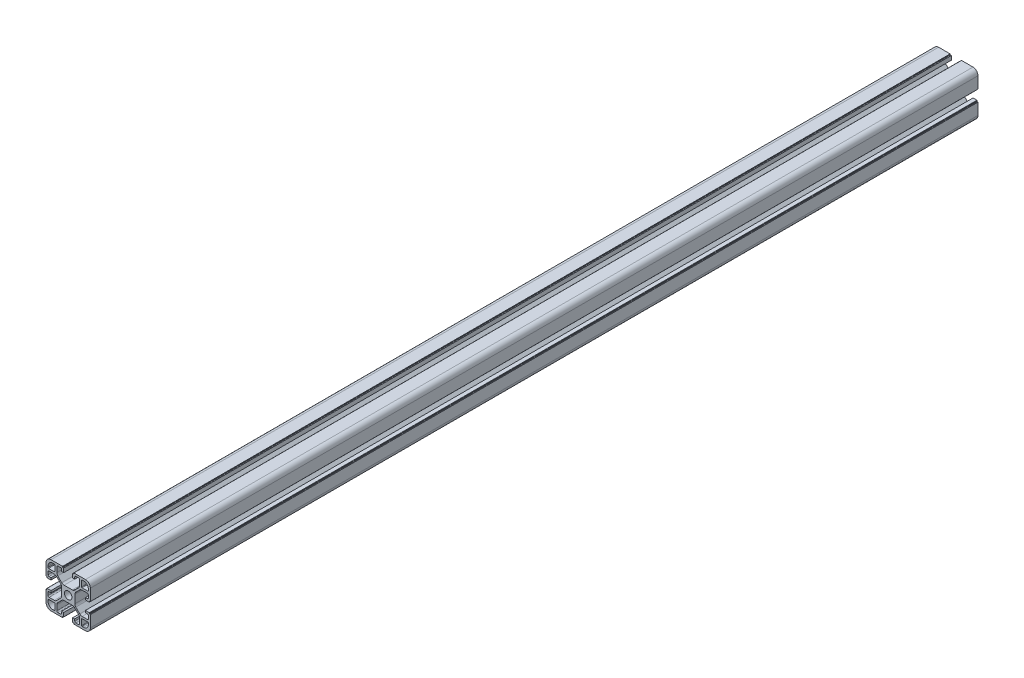
SolidWorks part; units mm, degrees
ref_plane "Front Plane" through (0, 0, 0) normal (0, 0, 1) x (1, 0, 0)
ref_plane "Top Plane" through (0, 0, 0) normal (0, 1, 0) x (1, 0, 0)
ref_plane "Right Plane" through (0, 0, 0) normal (1, 0, 0) x (0, 0, -1)
sketch "Sketch2" plane through (0, 0, 0) normal (0, 0, 1) x (1, 0, 0)
  line L0 (84.1702, 31.7204) -> (84.1702, 42.1204)
  line L1 (44.1702, 62.7204) -> (44.1702, 52.3204)
  line L2 (48.6702, 27.2204) -> (59.0702, 27.2204)
  line L3 (79.6702, 67.2204) -> (69.2702, 67.2204)
  line L4 (84.1702, 52.3204) -> (84.1702, 62.7204)
  line L6 (44.1702, 42.1204) -> (44.1702, 31.7204)
  line L7 (69.2702, 27.2204) -> (79.6702, 27.2204)
  line L10 (44.1702, 42.1204) -> (44.7702, 42.1204)
  line L11 (44.9702, 42.3204) -> (44.9702, 42.9204)
  line L12 (48.6702, 43.1204) -> (45.1702, 43.1204)
  line L13 (48.6702, 41.3204) -> (48.6702, 43.1204)
  line L14 (46.9702, 41.3204) -> (48.6702, 41.3204)
  line L15 (45.9702, 37.9704) -> (45.9702, 40.3204)
  line L16 (51.6169, 36.9704) -> (46.9702, 36.9704)
  line L17 (57.2915, 41.4024) -> (53.7382, 37.8491)
  line L18 (58.1702, 50.9171) -> (58.1702, 43.5237)
  line L19 (53.7382, 56.5917) -> (57.2915, 53.0384)
  line L20 (46.9702, 57.4704) -> (51.6169, 57.4704)
  line L21 (45.9702, 54.1204) -> (45.9702, 56.4704)
  line L22 (48.6702, 53.1204) -> (46.9702, 53.1204)
  line L23 (48.6702, 51.3204) -> (48.6702, 53.1204)
  line L24 (45.1702, 51.3204) -> (48.6702, 51.3204)
  line L25 (44.9702, 51.5204) -> (44.9702, 52.1204)
  line L26 (44.7702, 52.3204) -> (44.1702, 52.3204)
  line L28 (59.0702, 67.2204) -> (48.6702, 67.2204)
  line L29 (59.0702, 67.2204) -> (59.0702, 66.6204)
  line L30 (59.2702, 66.4204) -> (60.0702, 66.4204)
  line L31 (60.0702, 62.7204) -> (60.0702, 66.4204)
  line L32 (58.2702, 62.7204) -> (60.0702, 62.7204)
  line L33 (58.2702, 64.4204) -> (58.2702, 62.7204)
  line L34 (54.9202, 65.4204) -> (57.2702, 65.4204)
  line L35 (53.9202, 59.7737) -> (53.9202, 64.4204)
  line L36 (58.3522, 54.0991) -> (54.7989, 57.6524)
  line L37 (67.8669, 53.2204) -> (60.4735, 53.2204)
  line L38 (73.5415, 57.6524) -> (69.9882, 54.0991)
  line L39 (74.4202, 64.4204) -> (74.4202, 59.7737)
  line L40 (71.0702, 65.4204) -> (73.4202, 65.4204)
  line L41 (70.0702, 62.7204) -> (70.0702, 64.4204)
  line L42 (68.2702, 62.7204) -> (70.0702, 62.7204)
  line L43 (68.2702, 66.2204) -> (68.2702, 62.7204)
  line L44 (68.4702, 66.4204) -> (69.2702, 66.4204)
  line L45 (69.2702, 66.4204) -> (69.2702, 67.2204)
  line L48 (84.1702, 52.3204) -> (83.5702, 52.3204)
  line L49 (83.3702, 52.1204) -> (83.3702, 51.5204)
  line L50 (79.6702, 51.3204) -> (83.1702, 51.3204)
  line L51 (79.6702, 53.1204) -> (79.6702, 51.3204)
  line L52 (81.3702, 53.1204) -> (79.6702, 53.1204)
  line L53 (82.3702, 56.4704) -> (82.3702, 54.1204)
  line L54 (76.7235, 57.4704) -> (81.3702, 57.4704)
  line L55 (71.0489, 53.0384) -> (74.6022, 56.5917)
  line L56 (70.1702, 43.5237) -> (70.1702, 50.9171)
  line L57 (74.6022, 37.8491) -> (71.0489, 41.4024)
  line L58 (81.3702, 36.9704) -> (76.7235, 36.9704)
  line L59 (82.3702, 40.3204) -> (82.3702, 37.9704)
  line L60 (79.6702, 41.3204) -> (81.3702, 41.3204)
  line L61 (79.6702, 43.1204) -> (79.6702, 41.3204)
  line L62 (83.1702, 43.1204) -> (79.6702, 43.1204)
  line L63 (83.3702, 42.9204) -> (83.3702, 42.3204)
  line L64 (83.5702, 42.1204) -> (84.1702, 42.1204)
  line L67 (69.2702, 27.2204) -> (69.2702, 27.8204)
  line L68 (69.0702, 28.0204) -> (68.4702, 28.0204)
  line L69 (68.2702, 31.7204) -> (68.2702, 28.2204)
  line L70 (70.0702, 31.7204) -> (68.2702, 31.7204)
  line L71 (70.0702, 30.0204) -> (70.0702, 31.7204)
  line L72 (73.4202, 29.0204) -> (71.0702, 29.0204)
  line L73 (74.4202, 34.6671) -> (74.4202, 30.0204)
  line L74 (69.9882, 40.3417) -> (73.5415, 36.7884)
  line L75 (60.4735, 41.2204) -> (67.8669, 41.2204)
  line L76 (54.7989, 36.7884) -> (58.3522, 40.3417)
  line L77 (53.9202, 30.0204) -> (53.9202, 34.6671)
  line L78 (57.2702, 29.0204) -> (54.9202, 29.0204)
  line L79 (58.2702, 31.7204) -> (58.2702, 30.0204)
  line L80 (60.0702, 31.7204) -> (58.2702, 31.7204)
  line L81 (60.0702, 28.2204) -> (60.0702, 31.7204)
  line L82 (59.8702, 28.0204) -> (59.2702, 28.0204)
  line L83 (59.0702, 27.8204) -> (59.0702, 27.2204)
  line L84 (82.3702, 34.6704) -> (82.3702, 33.5204)
  line L85 (76.7202, 35.1704) -> (81.8702, 35.1704)
  line L86 (76.2202, 29.5204) -> (76.2202, 34.6704)
  line L87 (77.8702, 29.0204) -> (76.7202, 29.0204)
  line L88 (51.6202, 29.0204) -> (50.4702, 29.0204)
  line L89 (52.1202, 34.6704) -> (52.1202, 29.5204)
  line L90 (46.4702, 35.1704) -> (51.6202, 35.1704)
  line L91 (45.9702, 33.5204) -> (45.9702, 34.6704)
  line L92 (45.9702, 59.7704) -> (45.9702, 60.9204)
  line L93 (51.6202, 59.2704) -> (46.4702, 59.2704)
  line L94 (52.1202, 64.9204) -> (52.1202, 59.7704)
  line L95 (50.4702, 65.4204) -> (51.6202, 65.4204)
  line L96 (76.7202, 65.4204) -> (77.8702, 65.4204)
  line L97 (76.2202, 59.7704) -> (76.2202, 64.9204)
  line L98 (81.8702, 59.2704) -> (76.7202, 59.2704)
  line L99 (82.3702, 60.9204) -> (82.3702, 59.7704)
  arc A0 (60.7702, 47.2204) -> (67.5702, 47.2204) centre (64.1702, 47.2204) ccw
  arc A1 (44.1702, 31.7204) -> (48.6702, 27.2204) centre (48.6702, 31.7204) ccw
  arc A2 (44.7702, 42.1204) -> (44.9702, 42.3204) centre (44.7702, 42.3204) ccw
  arc A3 (45.1702, 43.1204) -> (44.9702, 42.9204) centre (45.1702, 42.9204) ccw
  arc A4 (46.9702, 41.3204) -> (45.9702, 40.3204) centre (46.9702, 40.3204) ccw
  arc A5 (45.9702, 37.9704) -> (46.9702, 36.9704) centre (46.9702, 37.9704) ccw
  arc A6 (51.6169, 36.9704) -> (53.7382, 37.8491) centre (51.6169, 39.9704) ccw
  arc A7 (57.2915, 41.4024) -> (58.1702, 43.5237) centre (55.1702, 43.5237) ccw
  arc A8 (58.1702, 50.9171) -> (57.2915, 53.0384) centre (55.1702, 50.9171) ccw
  arc A9 (53.7382, 56.5917) -> (51.6169, 57.4704) centre (51.6169, 54.4704) ccw
  arc A10 (46.9702, 57.4704) -> (45.9702, 56.4704) centre (46.9702, 56.4704) ccw
  arc A11 (45.9702, 54.1204) -> (46.9702, 53.1204) centre (46.9702, 54.1204) ccw
  arc A12 (44.9702, 51.5204) -> (45.1702, 51.3204) centre (45.1702, 51.5204) ccw
  arc A13 (44.9702, 52.1204) -> (44.7702, 52.3204) centre (44.7702, 52.1204) ccw
  arc A14 (48.6702, 67.2204) -> (44.1702, 62.7204) centre (48.6702, 62.7204) ccw
  arc A15 (59.0702, 66.6204) -> (59.2702, 66.4204) centre (59.2702, 66.6204) ccw
  arc A16 (58.2702, 64.4204) -> (57.2702, 65.4204) centre (57.2702, 64.4204) ccw
  arc A17 (54.9202, 65.4204) -> (53.9202, 64.4204) centre (54.9202, 64.4204) ccw
  arc A18 (53.9202, 59.7737) -> (54.7989, 57.6524) centre (56.9202, 59.7737) ccw
  arc A19 (58.3522, 54.0991) -> (60.4735, 53.2204) centre (60.4735, 56.2204) ccw
  arc A20 (67.8669, 53.2204) -> (69.9882, 54.0991) centre (67.8669, 56.2204) ccw
  arc A21 (73.5415, 57.6524) -> (74.4202, 59.7737) centre (71.4202, 59.7737) ccw
  arc A22 (74.4202, 64.4204) -> (73.4202, 65.4204) centre (73.4202, 64.4204) ccw
  arc A23 (71.0702, 65.4204) -> (70.0702, 64.4204) centre (71.0702, 64.4204) ccw
  arc A24 (68.4702, 66.4204) -> (68.2702, 66.2204) centre (68.4702, 66.2204) ccw
  arc A25 (84.1702, 62.7204) -> (79.6702, 67.2204) centre (79.6702, 62.7204) ccw
  arc A26 (83.5702, 52.3204) -> (83.3702, 52.1204) centre (83.5702, 52.1204) ccw
  arc A27 (83.1702, 51.3204) -> (83.3702, 51.5204) centre (83.1702, 51.5204) ccw
  arc A28 (81.3702, 53.1204) -> (82.3702, 54.1204) centre (81.3702, 54.1204) ccw
  arc A29 (82.3702, 56.4704) -> (81.3702, 57.4704) centre (81.3702, 56.4704) ccw
  arc A30 (76.7235, 57.4704) -> (74.6022, 56.5917) centre (76.7235, 54.4704) ccw
  arc A31 (71.0489, 53.0384) -> (70.1702, 50.9171) centre (73.1702, 50.9171) ccw
  arc A32 (70.1702, 43.5237) -> (71.0489, 41.4024) centre (73.1702, 43.5237) ccw
  arc A33 (74.6022, 37.8491) -> (76.7235, 36.9704) centre (76.7235, 39.9704) ccw
  arc A34 (81.3702, 36.9704) -> (82.3702, 37.9704) centre (81.3702, 37.9704) ccw
  arc A35 (82.3702, 40.3204) -> (81.3702, 41.3204) centre (81.3702, 40.3204) ccw
  arc A36 (83.3702, 42.9204) -> (83.1702, 43.1204) centre (83.1702, 42.9204) ccw
  arc A37 (83.3702, 42.3204) -> (83.5702, 42.1204) centre (83.5702, 42.3204) ccw
  arc A38 (79.6702, 27.2204) -> (84.1702, 31.7204) centre (79.6702, 31.7204) ccw
  arc A39 (69.2702, 27.8204) -> (69.0702, 28.0204) centre (69.0702, 27.8204) ccw
  arc A40 (68.2702, 28.2204) -> (68.4702, 28.0204) centre (68.4702, 28.2204) ccw
  arc A41 (70.0702, 30.0204) -> (71.0702, 29.0204) centre (71.0702, 30.0204) ccw
  arc A42 (73.4202, 29.0204) -> (74.4202, 30.0204) centre (73.4202, 30.0204) ccw
  arc A43 (74.4202, 34.6671) -> (73.5415, 36.7884) centre (71.4202, 34.6671) ccw
  arc A44 (69.9882, 40.3417) -> (67.8669, 41.2204) centre (67.8669, 38.2204) ccw
  arc A45 (60.4735, 41.2204) -> (58.3522, 40.3417) centre (60.4735, 38.2204) ccw
  arc A46 (54.7989, 36.7884) -> (53.9202, 34.6671) centre (56.9202, 34.6671) ccw
  arc A47 (53.9202, 30.0204) -> (54.9202, 29.0204) centre (54.9202, 30.0204) ccw
  arc A48 (57.2702, 29.0204) -> (58.2702, 30.0204) centre (57.2702, 30.0204) ccw
  arc A49 (59.8702, 28.0204) -> (60.0702, 28.2204) centre (59.8702, 28.2204) ccw
  arc A50 (59.2702, 28.0204) -> (59.0702, 27.8204) centre (59.2702, 27.8204) ccw
  arc A51 (82.3702, 34.6704) -> (81.8702, 35.1704) centre (81.8702, 34.6704) ccw
  arc A52 (76.7202, 35.1704) -> (76.2202, 34.6704) centre (76.7202, 34.6704) ccw
  arc A53 (76.2202, 29.5204) -> (76.7202, 29.0204) centre (76.7202, 29.5204) ccw
  arc A54 (77.8702, 29.0204) -> (82.3702, 33.5204) centre (77.8702, 33.5204) ccw
  arc A55 (51.6202, 29.0204) -> (52.1202, 29.5204) centre (51.6202, 29.5204) ccw
  arc A56 (52.1202, 34.6704) -> (51.6202, 35.1704) centre (51.6202, 34.6704) ccw
  arc A57 (46.4702, 35.1704) -> (45.9702, 34.6704) centre (46.4702, 34.6704) ccw
  arc A58 (45.9702, 33.5204) -> (50.4702, 29.0204) centre (50.4702, 33.5204) ccw
  arc A59 (45.9702, 59.7704) -> (46.4702, 59.2704) centre (46.4702, 59.7704) ccw
  arc A60 (51.6202, 59.2704) -> (52.1202, 59.7704) centre (51.6202, 59.7704) ccw
  arc A61 (52.1202, 64.9204) -> (51.6202, 65.4204) centre (51.6202, 64.9204) ccw
  arc A62 (50.4702, 65.4204) -> (45.9702, 60.9204) centre (50.4702, 60.9204) ccw
  arc A63 (76.7202, 65.4204) -> (76.2202, 64.9204) centre (76.7202, 64.9204) ccw
  arc A64 (76.2202, 59.7704) -> (76.7202, 59.2704) centre (76.7202, 59.7704) ccw
  arc A65 (81.8702, 59.2704) -> (82.3702, 59.7704) centre (81.8702, 59.7704) ccw
  arc A66 (82.3702, 60.9204) -> (77.8702, 65.4204) centre (77.8702, 60.9204) ccw
  arc A67 (67.5702, 47.2204) -> (60.7702, 47.2204) centre (64.1702, 47.2204) ccw
extrude "Boss-Extrude1" add sketch "Sketch2" along normal blind 800
